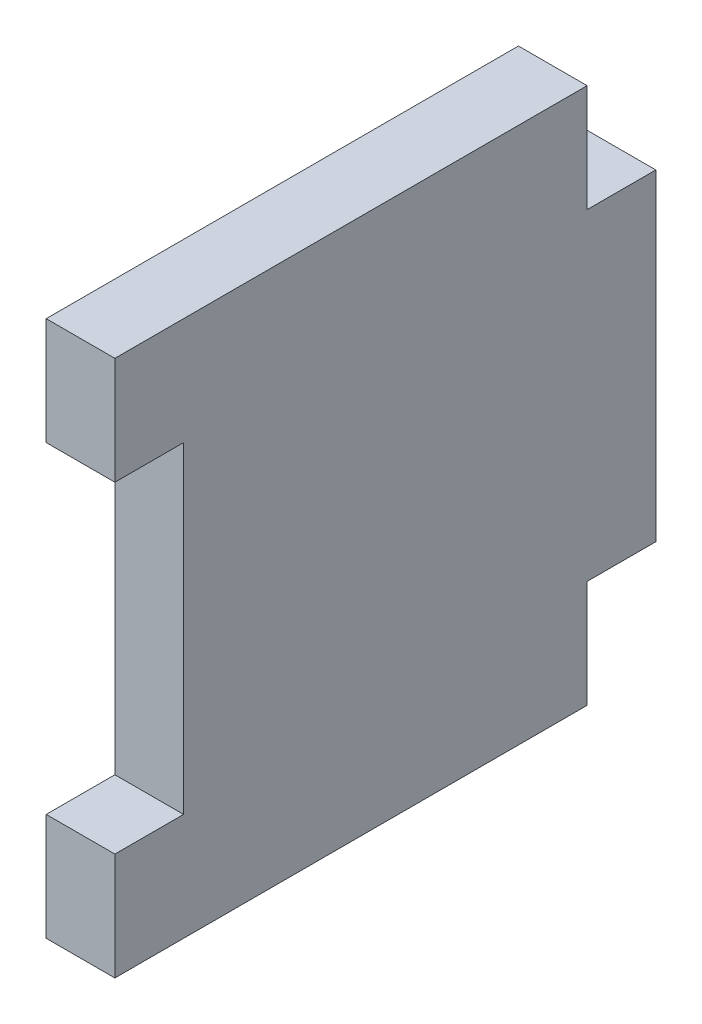
SolidWorks part; units mm, degrees
ref_plane "Front Plane" through (0, 0, 0) normal (0, 0, 1) x (1, 0, 0)
ref_plane "Top Plane" through (0, 0, 0) normal (0, 1, 0) x (1, 0, 0)
ref_plane "Right Plane" through (0, 0, 0) normal (1, 0, 0) x (0, 0, -1)
sketch "Sketch1" plane through (0, 0, 0) normal (1, 0, 0) x (0, 0, -1)
  line L0 (0, 0) -> (0, 15)
  line L1 (0, 15) -> (-3.2, 15)
  line L2 (-3.2, 15) -> (-3.2, 20)
  line L3 (-3.2, 20) -> (-25.2, 20)
  line L4 (-25.2, 20) -> (-25.2, 15)
  line L5 (-25.2, 15) -> (-22, 15)
  line L6 (-22, 15) -> (-22, 0)
  line L7 (-22, 0) -> (-25.2, 0)
  line L8 (-25.2, 0) -> (-25.2, -5)
  line L9 (-25.2, -5) -> (-3.2, -5)
  line L10 (-3.2, -5) -> (-3.2, 0)
  line L11 (-3.2, 0) -> (0, 0)
  dimension "D1" = 15
  dimension "D2" = 3.2
  dimension "D3" = 3.2
  dimension "D4" = 25
  dimension "D5" = 22
extrude "Boss-Extrude1" add sketch "Sketch1" along normal blind 3.2
